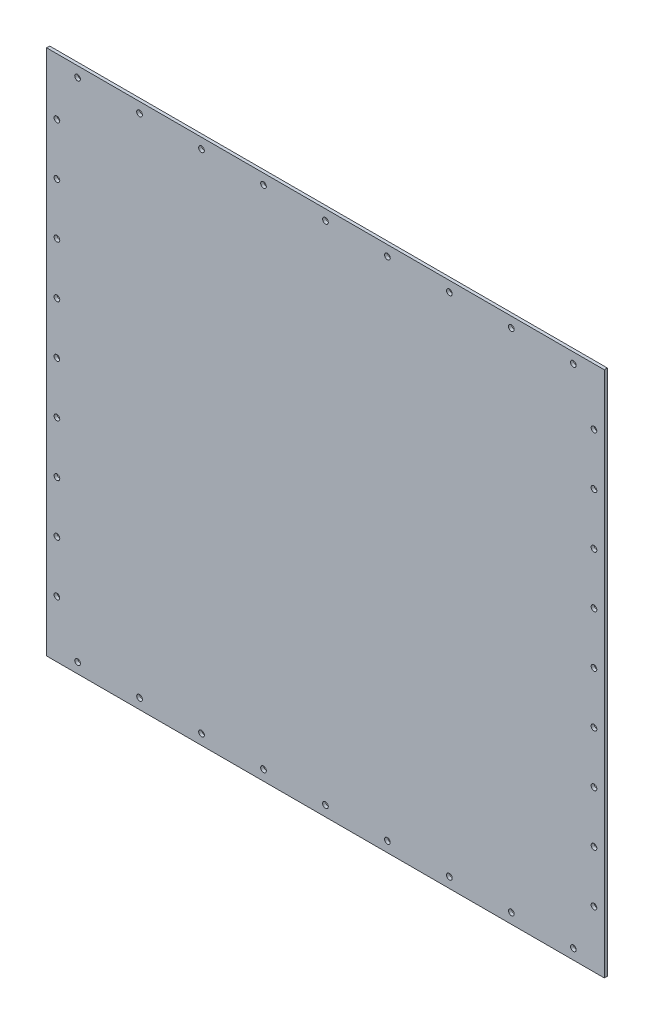
SolidWorks part; units mm, degrees
ref_plane "Front Plane" through (0, 0, 0) normal (0, 0, 1) x (1, 0, 0)
ref_plane "Top Plane" through (0, 0, 0) normal (0, 1, 0) x (1, 0, 0)
ref_plane "Right Plane" through (0, 0, 0) normal (1, 0, 0) x (0, 0, -1)
sketch "Sketch1" plane through (0, 0, 0) normal (0, 0, 1) x (1, 0, 0)
  line L1 (0, 0) -> (540, 0)
  line L2 (0, 0) -> (0, 510)
  line L3 (0, 510) -> (540, 510)
  line L4 (540, 0) -> (540, 510)
  dimension "D1" = 540
  dimension "D2" = 510
extrude "Boss-Extrude1" add sketch "Sketch1" along normal blind 3
sketch "Sketch2" plane through (0, 0, 3) normal (0, 0, 1) x (1, 0, 0)
  line L0 (10, 510) -> (10, 0) construction
  line L1 (540, 510) -> (0, 510) construction
  line L2 (0, 0) -> (540, 0) construction
  line L3 (0, 510) -> (0, 0) construction
  line L4 (0, 10) -> (540, 10) construction
  line L5 (540, 0) -> (540, 510) construction
  point P4 (270, 10)
  point P13 (10, 255)
  dimension "D1" = 10
  dimension "D2" = 10
hole_wizard "M5 Clearance Hole1" positions "Sketch3" profile "Sketch4" hole size "M5" standard "ANSI Metric" end condition through all
sketch "Sketch3" plane through (0, 0, 3) normal (0, 0, 1) x (1, 0, 0)
  point P0 (10, 255)
sketch "Sketch4" plane through (10, 255, 3) normal (1, 0, 0) x (0, -1, 0)
  line L0 (0, 0) -> (0, 3)
  line L1 (0, 3) -> (2.75, 3)
  line L2 (2.75, 3) -> (2.75, 0)
  line L5 (2.75, 0) -> (0, 0)
  line L11 (0, -6.35) -> (0, 107.95) construction
  dimension "Thru Hole Dia." = 5.5
  dimension "Thru Hole Depth" = 3
pattern_linear "LPattern1" count 5 spacing 50 along (0, 1, 0) of "M5 Clearance Hole1"
pattern_linear "LPattern2" count 5 spacing 50 along (0, -1, 0) of "M5 Clearance Hole1"
hole_wizard "M5 Clearance Hole2" positions "Sketch5" profile "Sketch6" hole size "M5" standard "ANSI Metric" end condition through all
sketch "Sketch5" plane through (0, 0, 3) normal (0, 0, 1) x (1, 0, 0)
  point P0 (270, 10)
sketch "Sketch6" plane through (270, 10, 3) normal (1, 0, 0) x (0, -1, 0)
  line L0 (0, 0) -> (0, 3)
  line L1 (0, 3) -> (2.75, 3)
  line L2 (2.75, 3) -> (2.75, 0)
  line L5 (2.75, 0) -> (0, 0)
  line L11 (0, -6.35) -> (0, 107.95) construction
  dimension "Thru Hole Dia." = 5.5
  dimension "Thru Hole Depth" = 3
pattern_linear "LPattern3" count 5 spacing 60 along (1, 0, 0) of "M5 Clearance Hole2"
pattern_linear "LPattern4" count 5 spacing 60 along (-1, 0, 0) of "M5 Clearance Hole2"
ref_plane "Plane1" through (0, 255, 0) normal (0, 1, 0) x (1, 0, 0)
ref_plane "Plane2" through (270, 0, 0) normal (-1, 0, 0) x (0, 0, 1)
mirror "Mirror1" about plane through (0, 255, 0) normal (0, 1, 0) of "LPattern3", "LPattern4", "M5 Clearance Hole2"
mirror "Mirror2" about plane through (270, 0, 0) normal (-1, 0, 0) of "LPattern1", "LPattern2", "M5 Clearance Hole1"
